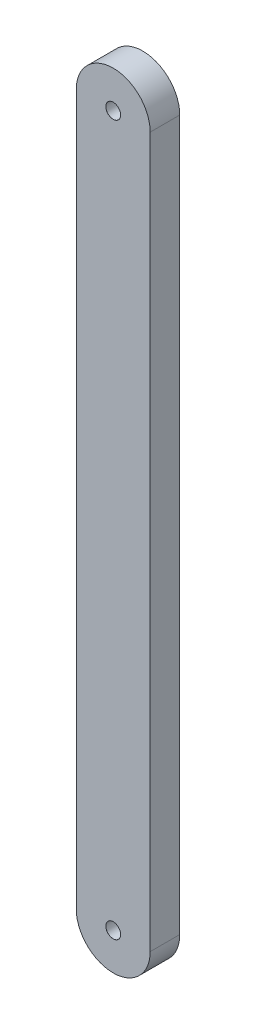
SolidWorks part; units mm, degrees
material "Alloy Steel"
ref_plane "Front Plane" through (0, 0, 0) normal (0, 0, 1) x (1, 0, 0)
ref_plane "Top Plane" through (0, 0, 0) normal (0, 1, 0) x (1, 0, 0)
ref_plane "Right Plane" through (0, 0, 0) normal (1, 0, 0) x (0, 0, -1)
sketch "Sketch2" plane through (0, 0, 0) normal (0, 0, 1) x (1, 0, 0)
  line L0 (-50, -240) -> (-50, 240)
  line L1 (0, 240) -> (0, -240)
  arc A0 (-50, 240) -> (0, 240) centre (-25, 240) cw
  arc A1 (0, -240) -> (-50, -240) centre (-25, -240) cw
  dimension "D1" = 480
  dimension "D2" = 50
extrude "Boss-Extrude1" add sketch "Sketch2" along normal blind 20
hole_wizard "Ø10.0mm Dowel Hole1" positions "Sketch3" profile "Sketch4" hole size "Ø10.0" standard "ANSI Metric" end condition through all
sketch "Sketch3" plane through (0, 0, 20) normal (0, 0, 1) x (1, 0, 0)
  point P0 (-25, 240)
  point P3 (-25, -240)
sketch "Sketch4" plane through (-25, 240, 20) normal (1, 0, 0) x (0, -1, 0)
  line L0 (0, 0) -> (0, 20)
  line L1 (0, 20) -> (5, 20)
  line L2 (5, 20) -> (5, 0.025)
  line L3 (5, 0.025) -> (5.025, 0)
  line L5 (5.025, 0) -> (0, 0)
  line L6 (-5, 0.025) -> (-5.025, 0) construction
  line L11 (0, -6.35) -> (0, 107.95) construction
  dimension "Thru Hole Dia." = 10
  dimension "Thru Hole Depth" = 20
  dimension "Near C'Sink Dia." = 10.05
  dimension "Near C'Sink Angle" = 90
